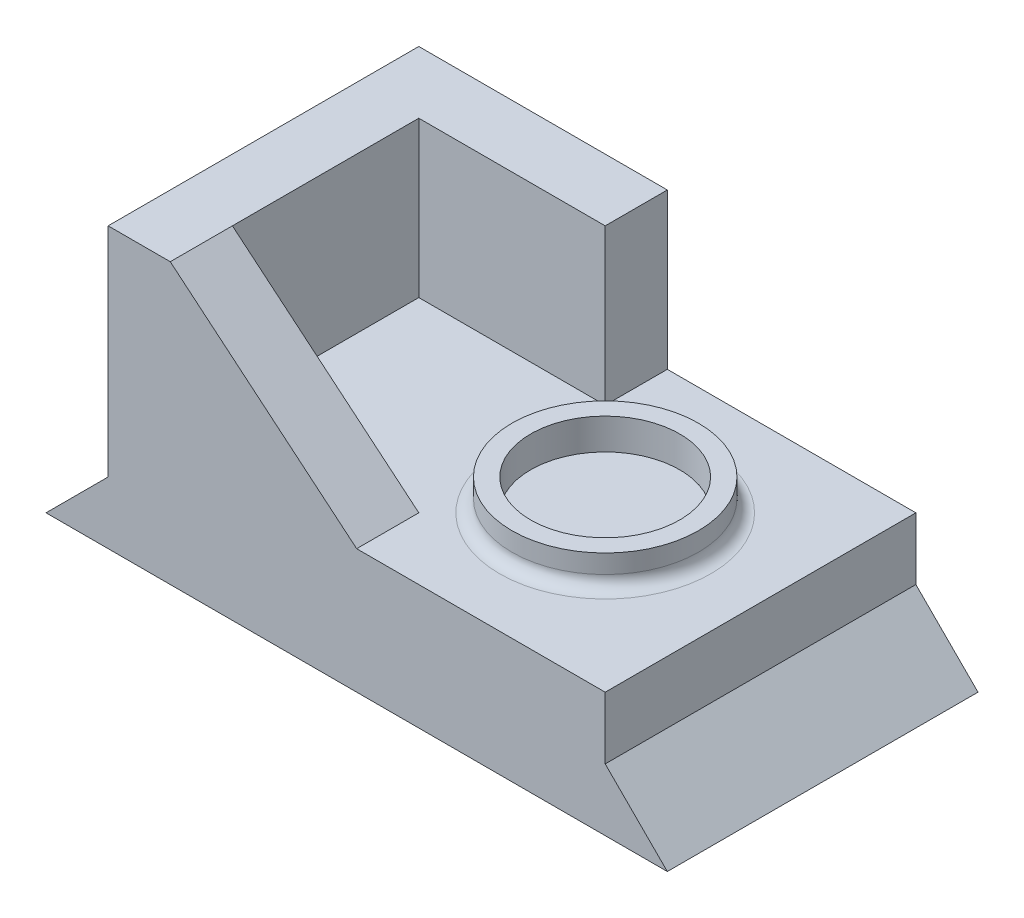
SolidWorks part; units mm, degrees
material "Alliage 1060"
ref_plane "Plan de face" through (0, 0, 0) normal (0, 0, 1) x (1, 0, 0)
ref_plane "Plan de dessus" through (0, 0, 0) normal (0, 1, 0) x (1, 0, 0)
ref_plane "Plan de droite" through (0, 0, 0) normal (1, 0, 0) x (0, 0, -1)
sketch "Esquisse2" plane through (0, 0, 0) normal (0, 0, 1) x (1, 0, 0)
  line L0 (0, 0) -> (100, 0)
  line L1 (100, 0) -> (90, 10)
  line L2 (90, 10) -> (10, 10)
  line L3 (10, 10) -> (0, 0)
  dimension "D1" = 100
  dimension "D2" = 10
  dimension "D3" = 10
  dimension "D4" = 10
extrude "Boss.-Extru.3" add sketch "Esquisse2" along normal blind 50
sketch "Esquisse3" plane through (0, 0, 50) normal (0, 0, 1) x (1, 0, 0)
  line L1 (10, 20) -> (90, 20)
  line L2 (10, 20) -> (10, 10)
  line L3 (10, 10) -> (90, 10)
  line L4 (90, 20) -> (90, 10)
  dimension "D1" = 10
  dimension "D2" = 80
extrude "Boss.-Extru.4" add sketch "Esquisse3" against normal blind 50
sketch "Esquisse4" plane through (0, 20, 0) normal (0, 1, 0) x (1, 0, 0)
  line L0 (90, -50) -> (10, -50) construction
  circle A0 centre (65, -25) radius 12
  circle A1 centre (65, -25) radius 15
  dimension "D3" = 24
  dimension "D4" = 30
  dimension "D1" = 25
  dimension "D2" = 35
extrude "Boss.-Extru.5" add sketch "Esquisse4" along normal blind 5
fillet "Congé1" radius 2 1 edges at (65, 20, 40)
sketch "Esquisse5" plane through (0, 20, 0) normal (0, 1, 0) x (1, 0, 0)
  line L0 (90, -50) -> (10, -50) construction
  line L1 (10, 0) -> (50, 0)
  line L3 (20, -10) -> (50, -10)
  line L4 (50, 0) -> (50, -10)
  line L5 (10, 0) -> (20, 0)
  line L6 (10, 0) -> (10, -50)
  line L7 (10, -50) -> (20, -50)
  line L8 (20, -10) -> (20, -50)
  line M6 (10, -50) -> (90, -50)
  line M8 (90, 0) -> (10, 0)
  line M9 (10, 0) -> (10, -50)
  dimension "D1" = 10
  dimension "D2" = 10
  dimension "D3" = 30
extrude "Boss.-Extru.6" add sketch "Esquisse5" along normal blind 25 contours L8 L3 L4 L1 M8 M9 M6
sketch "Esquisse6" plane through (0, 0, 50) normal (0, 0, 1) x (1, 0, 0)
  line L0 (20, 45) -> (50, 20)
  line L1 (20, 20) -> (50, 20) construction
  line L2 (50, 20) -> (20, 20)
  line L3 (20, 20) -> (20, 45)
  dimension "D1" = 30
extrude "Boss.-Extru.7" add sketch "Esquisse6" against normal blind 10
